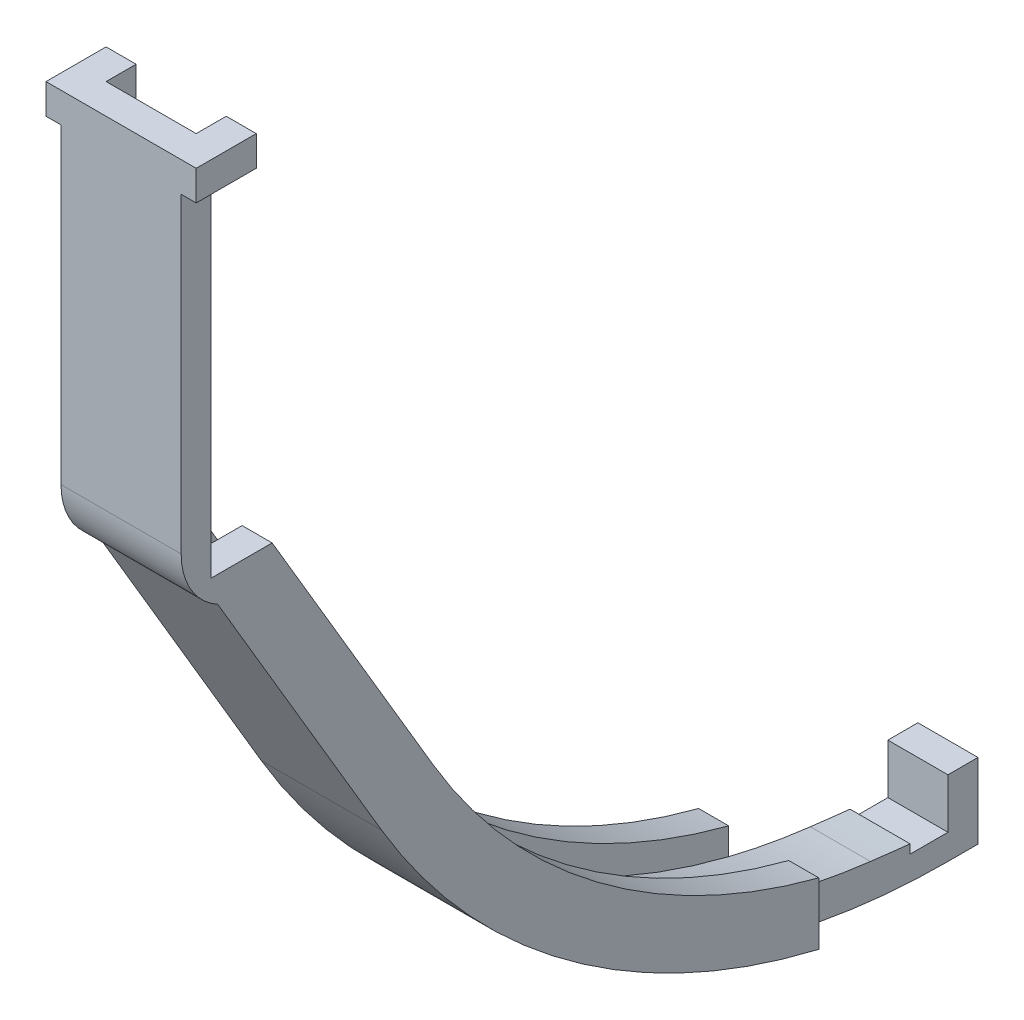
SolidWorks part; units mm, degrees
ref_plane "Front Plane" through (0, 0, 0) normal (0, 0, 1) x (1, 0, 0)
ref_plane "Top Plane" through (0, 0, 0) normal (0, 1, 0) x (1, 0, 0)
ref_plane "Right Plane" through (0, 0, 0) normal (1, 0, 0) x (0, 0, -1)
sketch "Sketch1" plane through (0, 0, 0) normal (0, 1, 0) x (1, 0, 0)
  circle A0 centre (0, 0) radius 30
  dimension "D1" = 60
sketch "Sketch3" plane through (0, 0, 0) normal (1, 0, 0) x (0, 0, -1)
  line L0 (0, 16.1146) -> (0, -58.8622) construction
sketch "Sketch2" plane through (0, 0, 0) normal (1, 0, 0) x (0, 0, -1)
  line L1 (30, 0) -> (-30, 0) construction
  line L2 (0, -50.8) -> (-30, 0)
  line L4 (0, 0) -> (0, -50.8)
  line L5 (-30, 0) -> (0, 0)
  dimension "D1" = 30
revolve "Revolve1" add sketch "Sketch2" angle 360 about L4
sketch "Sketch4" plane through (0, 0, 0) normal (1, 0, 0) x (0, 0, -1)
  line L0 (0, -45.72) -> (-24.92, 0)
  line L1 (0, 16.1146) -> (0, -58.8622) construction
  line L2 (30, 0) -> (-30, 0) construction
  line L3 (-24.92, 0) -> (0, 0)
  line L4 (0, 0) -> (0, -45.72)
  dimension "D1" = 5.08
  dimension "D2" = 5.08
revolve "Cut-Revolve1" cut sketch "Sketch4" angle 360 about L0
sketch "Sketch5" plane through (0, 0, 0) normal (1, 0, 0) x (0, 0, -1)
  line L0 (0, 16.1146) -> (0, -58.8622) construction
  line L1 (6.44, -39.8949) -> (-6.44, -39.8949)
  line L2 (6.44, -39.8949) -> (6.44, -55.7296)
  line L3 (6.44, -55.7296) -> (-6.44, -55.7296)
  line L4 (-6.44, -39.8949) -> (-6.44, -55.7296)
  line L5 (0, -50.8) -> (30, 0) construction
  line L6 (-24.92, 0) -> (0, -45.72) construction
  line L7 (30, 0) -> (-30, 0) construction
  line L8 (0, -45.72) -> (24.92, 0) construction
  point P4 (0, -39.8949)
  point P7 (3.175, -39.8949)
  point P18 (-3.175, -39.8949)
  dimension "D1" = 6.35
  dimension "D2" = 5.08
  dimension "D3" = 5.08
extrude "Cut-Extrude2" cut sketch "Sketch5" against normal mid plane 15.24
ref_plane "Plane1" through (0, 0, 30) normal (0, 0, 1) x (1, 0, 0)
sketch "Sketch11" plane through (0, 0, 30) normal (0, 0, 1) x (1, 0, 0)
  line L0 (30, 0) -> (-30, 0) construction
  line L1 (6.35, 0) -> (3.175, 0)
  line L2 (6.35, 0) -> (6.35, -3.175)
  line L3 (6.35, -3.175) -> (3.175, -3.175)
  line L4 (3.175, 0) -> (3.175, -3.175)
  line L5 (3.175, -3.175) -> (-3.175, -3.175) construction
  line L6 (-3.175, 0) -> (-6.35, 0)
  line L7 (-3.175, 0) -> (-3.175, -3.175)
  line L8 (-3.175, -3.175) -> (-6.35, -3.175)
  line L9 (-6.35, 0) -> (-6.35, -3.175)
  point P10 (0, -3.175)
  dimension "D1" = 3.175
  dimension "D2" = 3.175
  dimension "D3" = 6.35
extrude "Cut-Extrude6" cut sketch "Sketch11" against normal up to next
sketch "Sketch6" plane through (0, 0, 0) normal (1, 0, 0) x (0, 0, -1)
  line L0 (-7.3746, -39.8949) -> (11.5628, -71.9623)
  line L1 (74.61, -101.6) -> (74.61, -100.0125)
  line L2 (74.61, -100.0125) -> (77.785, -100.0125)
  line L3 (77.785, -100.0125) -> (77.785, -107.95)
  line L5 (0, -39.8949) -> (17.0305, -68.7333)
  line L6 (-30, 0) -> (-6.44, -39.8949) construction
  line L7 (30, 0) -> (-30, 0) construction
  line L8 (0, 16.1146) -> (0, -58.8622) construction
  line L11 (0, -39.8949) -> (-23.56, 0)
  line L12 (0, -39.8949) -> (-7.3746, -39.8949)
  line L13 (-23.56, 0) -> (-30.9346, 0)
  line L14 (-7.3746, -39.8949) -> (-30.9346, 0)
  line L15 (-6.44, -39.8949) -> (6.44, -39.8949) construction
  line L16 (74.61, -107.95) -> (77.785, -107.95)
  arc A0 (11.5628, -71.9623) -> (54.61, -105.1656) centre (74.61, -34.7297) ccw
  arc A1 (17.0305, -68.7333) -> (74.61, -101.6) centre (74.61, -34.7297) ccw
  arc A2 (54.61, -105.1656) -> (74.61, -107.95) centre (74.61, -34.7297) ccw
  dimension "D1" = 3.175
  dimension "D3" = 1.5875
  dimension "D2" = 6.35
  dimension "D4" = 6.35
  dimension "D5" = 107.95
  dimension "D6" = 54.61
  dimension "D7" = 20
extrude "Boss-Extrude1" add sketch "Sketch6" along normal mid plane 12.7
sketch "Sketch7" plane through (0, 0, 0) normal (1, 0, 0) x (0, 0, -1)
  line L0 (-3.175, -39.8949) -> (14.6765, -70.1235)
  line L1 (17.0305, -68.7333) -> (0, -39.8949) construction
  line L2 (0, 16.1146) -> (0, -58.8622) construction
  line L3 (-3.175, -39.8949) -> (-26.735, 0)
  line L4 (30, 0) -> (-30, 0) construction
  line L5 (-1.0729, -39.8949) -> (0, -39.8949) construction
  line L8 (-23.56, 0) -> (-26.735, 0)
  line L9 (17.0305, -68.7333) -> (-23.56, 0)
  line L10 (74.61, -104.775) -> (74.61, -101.6)
  arc A0 (14.6765, -70.1235) -> (66.4142, -103.8497) centre (74.61, -34.7297) ccw
  arc A1 (17.0305, -68.7333) -> (74.61, -101.6) centre (74.61, -34.7297) ccw construction
  arc A4 (17.0305, -68.7333) -> (44.8862, -94.6307) centre (74.61, -34.7297) ccw
  arc A7 (66.4142, -103.8497) -> (74.61, -104.775) centre (153.2047, 628.1044) ccw
  arc A8 (17.0305, -68.7333) -> (74.61, -101.6) centre (74.61, -34.7297) ccw construction
  arc A9 (74.61, -101.6) -> (44.8862, -94.6307) centre (74.61, -34.7297) cw
  dimension "D1" = 3.175
  dimension "D2" = 3.175
extrude "Cut-Extrude4" cut sketch "Sketch7" against normal blind 3.175 contours L0 A0 A7 L10 A9 A4 L9 L8 L3
mirror "Mirror1" about plane through (0, 0, 0) normal (1, 0, 0) of "Cut-Extrude4"
sketch "Sketch9" plane through (0, 0, 0) normal (1, 0, 0) x (0, 0, -1)
  line L0 (0, 0) -> (-24.92, 0)
  line L1 (-24.92, 0) -> (-0.5365, -39.8949)
  line L2 (-1.0729, -39.8949) -> (0, -39.8949) construction
  line L3 (-0.5365, -39.8949) -> (0, -39.8949)
  line L4 (0, -39.8949) -> (0, 0)
  dimension "D1" = 24.92
revolve "Cut-Revolve2" cut sketch "Sketch9" angle 360 about L0
sketch "Sketch10" plane through (-6.35, 0, 0) normal (-1, 0, 0) x (0, 0, 1)
  line L0 (-74.61, -101.6) -> (-74.61, -100.0125) construction
  line L1 (-74.61, -101.4803) -> (-70.61, -101.4803)
  line L2 (-74.61, -101.4803) -> (-74.61, -104.775)
  line L3 (-74.61, -104.775) -> (-70.61, -104.775)
  line L4 (-70.61, -101.4803) -> (-70.61, -104.775)
  line L6 (-74.61, -104.775) -> (-70.61, -104.775)
  line L7 (-74.61, -104.775) -> (-74.61, -105.275)
  line L8 (-74.61, -105.275) -> (-70.61, -105.275)
  line L9 (-70.61, -104.775) -> (-70.61, -105.275)
  arc A0 (-74.61, -101.6) -> (-17.0305, -68.7333) centre (-74.61, -34.7297) ccw construction
  arc M9 (-17.0305, -68.7333) -> (-74.61, -101.6) centre (-74.61, -34.7297) cw
  dimension "D1" = 0.5
  dimension "D2" = 4
extrude "Cut-Extrude5" cut sketch "Sketch10" against normal through all contours L4 L2 L3 M9 | L9 L3 L7 L8
sketch "Sketch12" plane through (0, 0, 0) normal (-1, 0, 0) x (0, 0, 1)
  line L1 (30, 0) -> (-61.0259, 0)
  line L2 (-61.0259, 0) -> (-61.0259, -39.8949)
  line L6 (30, 0) -> (-30, 0) construction
  line L7 (29.3203, 0) -> (30.9346, 0) construction
  line L9 (-6.44, -39.8949) -> (-61.0259, -39.8949)
  line L10 (27.9452, -3.175) -> (6.44, -39.8949)
  line L11 (27.9452, -3.175) -> (30, 0)
  line L12 (-6.44, -39.8949) -> (6.44, -39.8949)
  line L13 (0, 16.1146) -> (0, -58.8622) construction
  dimension "D1" = 30
  dimension "D2" = 6.44
extrude "Cut-Extrude7" cut sketch "Sketch12" against normal mid plane 81.28
sketch "Sketch13" plane through (0, -13.5447, 22.9358) normal (0, -0.5085, 0.8611) x (1, 0, 0)
  line L1 (-6.35, 15.7303) -> (-28.6819, 15.7303)
  line L2 (-6.35, 15.7303) -> (-6.35, -41.1116)
  line L3 (-6.35, -41.1116) -> (-28.6819, -41.1116)
  line L4 (-28.6819, 15.7303) -> (-28.6819, -41.1116)
  line L5 (6.35, 15.7303) -> (27.8907, 15.7303)
  line L6 (6.35, 15.7303) -> (6.35, -42.7196)
  line L7 (6.35, -42.7196) -> (27.8907, -42.7196)
  line L8 (27.8907, 15.7303) -> (27.8907, -42.7196)
extrude "Cut-Extrude8" [suppressed] cut sketch "Sketch13" against normal through all
sketch "Sketch18" plane through (-6.35, 0, 0) normal (-1, 0, 0) x (0, 0, 1)
  line L0 (6.44, -39.8949) -> (6.44, 0)
  line L1 (30, 0) -> (-30, 0) construction
  line L2 (6.44, 0) -> (9.615, 0)
  line L3 (9.615, 0) -> (9.615, -34.4736)
  line L4 (27.9452, -3.175) -> (6.44, -39.8949) construction
  line L6 (9.615, -34.4736) -> (9.615, -36.1012)
  line L7 (-11.5628, -71.9623) -> (30.9346, 0) construction
  line L8 (5.7568, -42.6345) -> (6.44, -41.4775)
  line L9 (6.44, -41.4775) -> (6.44, -39.8949)
  arc A1 (9.615, -36.1012) -> (5.7568, -42.6345) centre (2.1544, -36.1012) cw
  point P14 (8.5784, -39.8949)
  dimension "D1" = 3.175
extrude "Boss-Extrude3" add sketch "Sketch18" against normal up to surface (12.7 mm away) up to face at (6.35, -69.0471, -31.7883)
sketch "Sketch19" plane through (-6.35, 0, 0) normal (-1, 0, 0) x (0, 0, 1)
  line L0 (9.615, 0) -> (9.615, -36.1012)
  line L1 (9.615, -36.1012) -> (30.9346, -36.1012)
  line L2 (30.9346, -36.1012) -> (30.9346, 0)
  line L3 (30.9346, 0) -> (9.615, 0)
  line L4 (-11.5628, -71.9623) -> (5.7568, -42.6345) construction
extrude "Cut-Extrude10" cut sketch "Sketch19" against normal through all
sketch "Sketch15" plane through (-6.35, 0, 0) normal (-1, 0, 0) x (0, 0, 1)
  line L0 (9.615, 0) -> (3.265, 0)
  line L1 (30, 0) -> (-30, 0) construction
  line L2 (3.265, 0) -> (3.265, -3.175)
  line L3 (3.265, -3.175) -> (9.615, -3.175)
  line L5 (9.615, -3.175) -> (9.615, 0)
  line L7 (9.615, -36.1012) -> (9.615, 0) construction
  dimension "D1" = 3.175
  dimension "D2" = 6.35
extrude "Boss-Extrude2" add sketch "Sketch15" along normal mid plane 3.175
mirror "Mirror2" about plane through (0, 0, 0) normal (1, 0, 0) of "Boss-Extrude2"
sketch "Sketch16" [suppressed] plane through (0, 0, 0) normal (0, 1, 0) x (1, 0, 0)
  line L0 (7.9375, -28.9309) -> (7.9375, -30.9346)
  line L1 (7.9375, -9.615) -> (7.9375, -3.265) construction
  line L2 (7.9375, -30.9346) -> (-7.9375, -30.9346)
  line L3 (-7.9375, -30.9346) -> (-7.9375, -28.9309)
  circle A0 centre (0, 0) radius 30
  circle A1 centre (0, 0) radius 30 construction
sketch "Sketch17" plane through (0, 0, -77.785) normal (0, 0, -1) x (-1, 0, 0)
  line L0 (-6.35, -68.7333) -> (-6.35, -101.4803) construction
  line L1 (-6.35, -70.6178) -> (-3.175, -70.6178)
  line L2 (-6.35, -70.6178) -> (-6.35, -107.95)
  line L3 (-6.35, -107.95) -> (-3.175, -107.95)
  line L4 (-3.175, -70.6178) -> (-3.175, -107.95)
  line L5 (-6.35, -107.95) -> (6.35, -107.95) construction
  line L6 (3.175, -68.7333) -> (3.175, -101.4803) construction
  line L7 (3.175, -70.6178) -> (6.35, -70.6178)
  line L8 (3.175, -70.6178) -> (3.175, -107.95)
  line L9 (3.175, -107.95) -> (6.35, -107.95)
  line L10 (6.35, -70.6178) -> (6.35, -107.95)
  line L11 (-3.175, -101.4803) -> (-3.175, -68.7333) construction
extrude "Cut-Extrude9" cut sketch "Sketch17" against normal blind 20
sketch "Sketch20" plane through (0, 0, 0) normal (0, 1, 0) x (1, 0, 0)
  line L0 (-3.175, 17.0305) -> (-3.175, 57.785) construction
  line L1 (3.175, 74.61) -> (-3.175, 74.61)
  line L2 (3.175, 74.61) -> (3.175, 70.61)
  line L3 (3.175, 70.61) -> (-3.175, 70.61)
  line L4 (-3.175, 74.61) -> (-3.175, 70.61)
  dimension "D1" = 4
